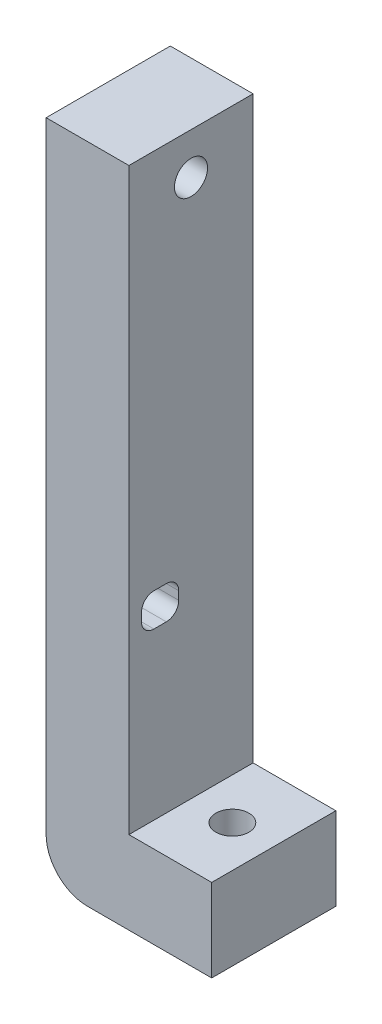
SolidWorks part; units mm, degrees
ref_plane "Front Plane" through (0, 0, 0) normal (0, 0, 1) x (1, 0, 0)
ref_plane "Top Plane" through (0, 0, 0) normal (0, 1, 0) x (1, 0, 0)
ref_plane "Right Plane" through (0, 0, 0) normal (1, 0, 0) x (0, 0, -1)
sketch "Sketch1" plane through (0, 0, 0) normal (0, 0, 1) x (1, 0, 0)
  line L0 (0, 20) -> (0, -10)
  line L1 (-10, -20) -> (10, -20)
  line L2 (-10, -20) -> (-10, 20)
  line L3 (-10, 20) -> (0, 20)
  line L4 (10, -20) -> (10, -10)
  line L5 (-10, -20) -> (0, 0) construction
  line L6 (-10, 20) -> (10, -20) construction
  line L7 (0, -10) -> (10, -10)
  point P0 (0, 0)
  dimension "D1" = 20
  dimension "D2" = 40
  dimension "D3" = 10
  dimension "D4" = 20
extrude "Boss-Extrude1" add sketch "Sketch1" along normal blind 15
fillet "Fillet1" radius 5 1 edges at (-10, -20, 7.5)
sketch "Sketch2" plane through (0, 20, 0) normal (0, 1, 0) x (1, 0, 0)
  line L4 (0, 0) -> (-10, 0)
  line L5 (-10, 0) -> (-10, -15)
  line L6 (-10, -15) -> (0, -15)
  line L7 (0, -15) -> (0, 0)
  line L8 (0, 0) -> (-10, 0)
  line L9 (-10, 0) -> (-10, -15)
  line L10 (-10, -15) -> (0, -15)
  line L11 (0, -15) -> (0, 0)
  dimension "D1" = 0
extrude "Boss-Extrude2" add sketch "Sketch2" along normal blind 40
sketch "Sketch3" plane through (0, -20, 0) normal (0, -1, 0) x (1, 0, 0)
  line L0 (5, 15) -> (5, 0) construction
  line L4 (-5, 15) -> (10, 15) construction
  line L5 (-5, 0) -> (10, 0) construction
  line L6 (10, 15) -> (10, 0) construction
  circle A0 centre (5, 7.5) radius 2
  dimension "D1" = 4
  dimension "D2" = 5
extrude "Cut-Extrude1" cut sketch "Sketch3" against normal through all
sketch "Sketch4" plane through (0, 0, 0) normal (1, 0, 0) x (0, 0, -1)
  line L0 (-10.48, 10) -> (-11.98, 10)
  line L1 (-13.48, 11.5) -> (-13.48, 12.5)
  line L2 (-11.98, 14) -> (-10.48, 14)
  line L3 (-8.98, 12.5) -> (-8.98, 11.5)
  line L4 (-15, -10) -> (-15, 60) construction
  line L5 (-15, 60) -> (0, 60) construction
  arc A0 (-13.48, 12.5) -> (-11.98, 14) centre (-11.98, 12.5) cw
  arc A1 (-10.48, 14) -> (-8.98, 12.5) centre (-10.48, 12.5) cw
  arc A2 (-13.48, 11.5) -> (-11.98, 10) centre (-11.98, 11.5) ccw
  arc A3 (-8.98, 11.5) -> (-10.48, 10) centre (-10.48, 11.5) cw
  point P13 (-8.98, 14)
  point P16 (-13.48, 10)
  point P19 (-8.98, 10)
  dimension "D5" = 1.5
  dimension "D6" = 1.5
  dimension "D1" = 1.52
  dimension "D2" = 4
  dimension "D3" = 46
  dimension "D4" = 4.5
extrude "Cut-Extrude2" cut sketch "Sketch4" against normal through all
sketch "Sketch5" plane through (-10, 0, 0) normal (-1, 0, 0) x (0, 0, 1)
  circle A0 centre (7.5, 55) radius 2
extrude "Cut-Extrude3" cut sketch "Sketch5" against normal through all
